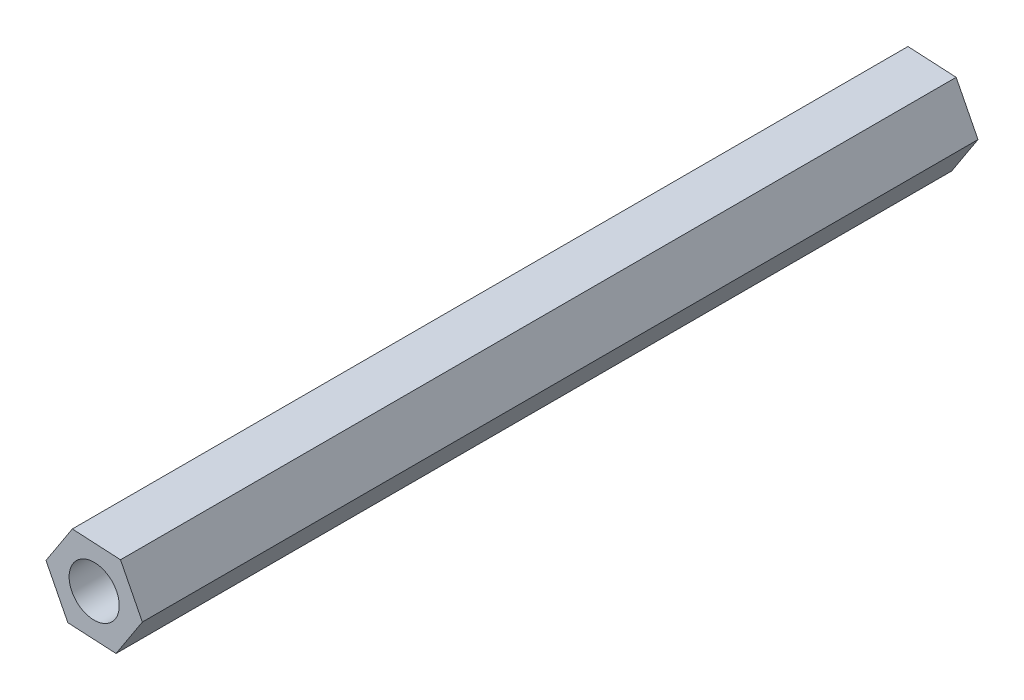
SolidWorks part; units mm, degrees
ref_plane "Front Plane" through (0, 0, 0) normal (0, 0, 1) x (1, 0, 0)
ref_plane "Top Plane" through (0, 0, 0) normal (0, 1, 0) x (1, 0, 0)
ref_plane "Right Plane" through (0, 0, 0) normal (1, 0, 0) x (0, 0, -1)
sketch "Sketch1" plane through (0, 0, 0) normal (0, 0, 1) x (1, 0, 0)
  line L1 (1.5755, 2.4189) -> (-1.3071, 2.5739)
  line L2 (-1.3071, 2.5739) -> (-2.8826, 0.1549)
  line L3 (-2.8826, 0.1549) -> (-1.5755, -2.4189)
  line L4 (-1.5755, -2.4189) -> (1.3071, -2.5739)
  line L5 (1.3071, -2.5739) -> (2.8826, -0.1549)
  line L6 (2.8826, -0.1549) -> (1.5755, 2.4189)
  circle A0 centre (0, 0) radius 2.5 construction
  dimension "D1" = 5
extrude "Boss-Extrude1" add sketch "Sketch1" along normal blind 50
sketch "Sketch2" plane through (0, 0, 0) normal (0, 0, -1) x (-1, 0, 0)
  circle A0 centre (0, 0) radius 1.5
  dimension "D1" = 3
extrude "Cut-Extrude1" cut sketch "Sketch2" against normal through all
